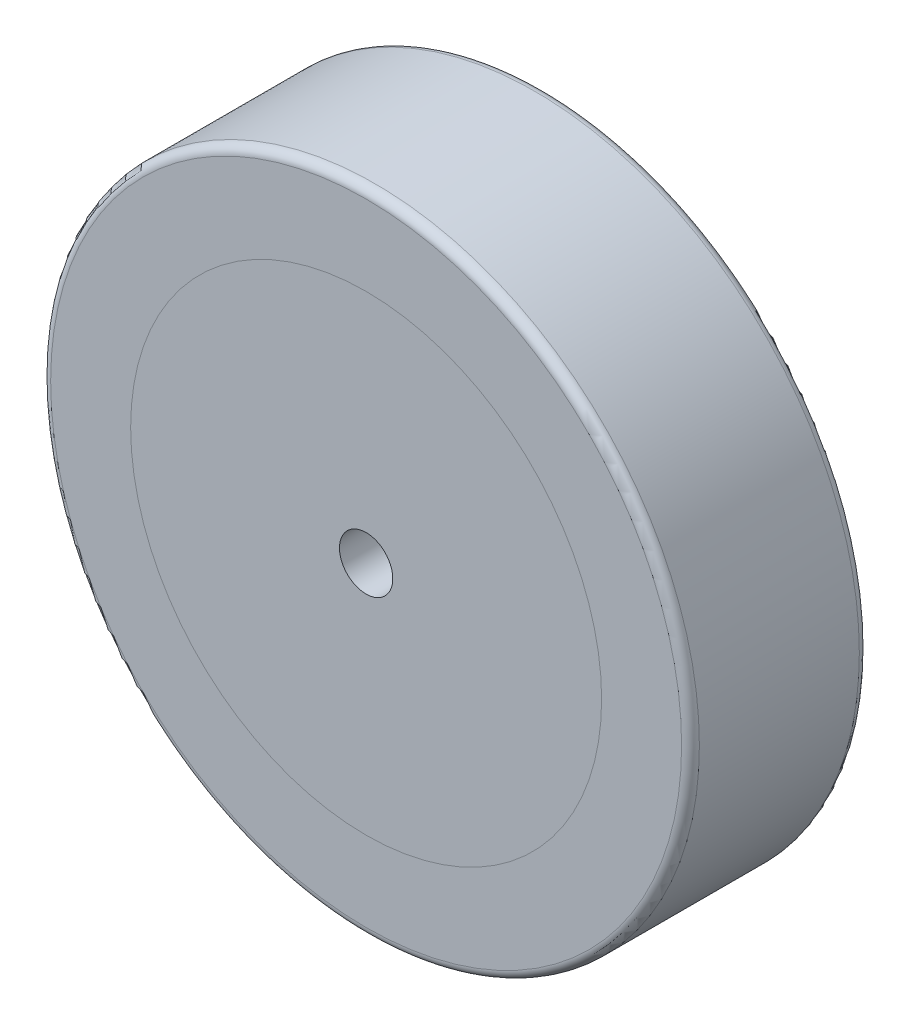
SolidWorks part; units mm, degrees
ref_plane "Plan de face" through (0, 0, 0) normal (0, 0, 1) x (1, 0, 0)
ref_plane "Plan de dessus" through (0, 0, 0) normal (0, 1, 0) x (1, 0, 0)
ref_plane "Plan de droite" through (0, 0, 0) normal (1, 0, 0) x (0, 0, -1)
sketch "Esquisse1" plane through (0, 0, 0) normal (0, 0, 1) x (1, 0, 0)
  circle A0 centre (0, 0) radius 36.5
  dimension "D1" = 73
extrude "Boss.-Extru.1" add sketch "Esquisse1" along normal blind 20
sketch "Esquisse2" plane through (0, 0, 20) normal (0, 0, 1) x (1, 0, 0)
  circle A0 centre (0, 0) radius 26.5
  dimension "D1" = 53
extrude "Enlèv. mat.-Extru.2" cut sketch "Esquisse2" against normal blind 20
sketch "Esquisse4" plane through (0, 0, 20) normal (0, 0, 1) x (1, 0, 0)
  circle A0 centre (0, 0) radius 26.5
  dimension "D1" = 53
extrude "Boss.-Extru.3" add sketch "Esquisse4" against normal blind 20 separate body
hole_wizard "Dégagement M81" positions "Esquisse10" profile "Esquisse9" hole size "M8" standard "ISO" end condition through all
sketch "Esquisse10" plane through (0, 0, 0) normal (0, 0, -1) x (-1, 0, 0)
  point P1 (0, 0)
sketch "Esquisse9" plane through (0, 0, 0) normal (1, 0, 0) x (0, 1, 0)
  line L0 (0, 0) -> (0, 20)
  line L1 (0, 20) -> (3, 20)
  line L2 (3, 20) -> (3, 0)
  line L5 (3, 0) -> (0, 0)
  line L11 (0, -6.35) -> (0, 107.95) construction
  dimension "Diamètre du perçage jusqu'au prochain" = 6
  dimension "Profondeur du perçage jusqu'au prochain" = 20
fillet "Congé1" radius 1 2 edges at (36.5, 0, 0) (36.5, 0, 20)
